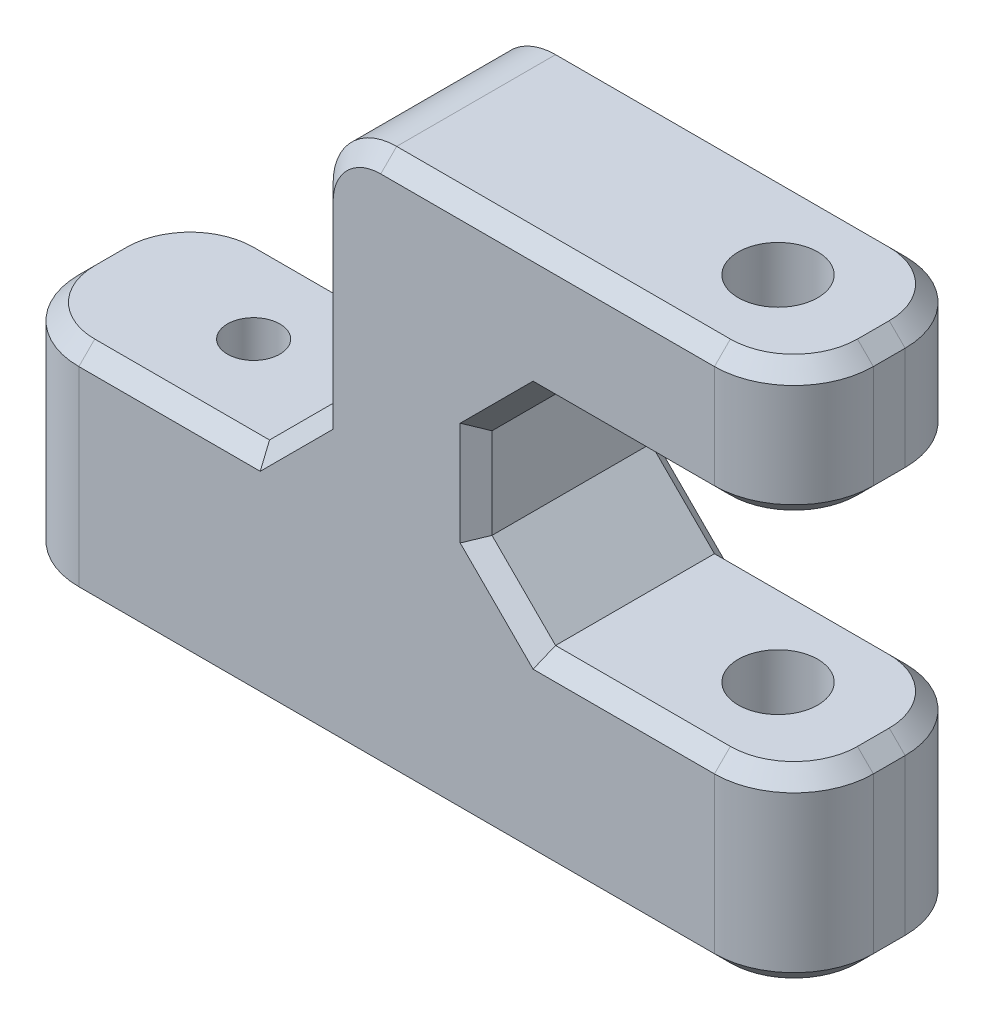
SolidWorks part; units mm, degrees
material "PLA"
ref_plane "Front Plane" through (0, 0, 0) normal (0, 0, 1) x (1, 0, 0)
ref_plane "Top Plane" through (0, 0, 0) normal (0, 1, 0) x (1, 0, 0)
ref_plane "Right Plane" through (0, 0, 0) normal (1, 0, 0) x (0, 0, -1)
sketch "Sketch1" plane through (0, 0, 0) normal (0, 0, 1) x (1, 0, 0)
  line L0 (0, 14) -> (0, 34)
  line L1 (0, 34) -> (30, 34)
  line L2 (30, 34) -> (30, 25.5)
  line L3 (30, 25.5) -> (10, 25.5)
  line L4 (10, 25.5) -> (10, 11.8)
  line L5 (10, 11.8) -> (30, 11.8)
  line L6 (30, 11.8) -> (30, 0)
  line L7 (30, 0) -> (0, 0)
  line L8 (2.9482, 34) -> (2.9482, 0) construction
  line L9 (0, 14) -> (-20, 14)
  line L10 (-20, 14) -> (-20, 0)
  line L11 (-20, 0) -> (0, 0)
  line L12 (2.9482, 18.65) -> (37.0838, 18.65) construction
  point P16 (10, 18.65)
  point P17 (0, 0)
  dimension "D1" = 34
  dimension "D2" = 13.7
  dimension "D3" = 10
  dimension "D4" = 30
  dimension "D5" = 20
  dimension "D6" = 20
extrude "Boss-Extrude1" add sketch "Sketch1" along normal mid plane 12
sketch "Sketch2" plane through (0, 14, 0) normal (0, 1, 0) x (1, 0, 0)
  line L0 (0, 0) -> (-20, 0) construction
  line L1 (-20, -6) -> (-20, 6) construction
  circle A0 centre (-10, 0) radius 1.65
  dimension "D1" = 3.3
extrude "Cut-Extrude1" cut sketch "Sketch2" against normal blind 20
sketch "Sketch3" plane through (0, 11.8, 0) normal (0, 1, 0) x (1, 0, 0)
  line L0 (30, 0) -> (0, 0) construction
  line L1 (30, -6) -> (30, 6) construction
  circle A0 centre (23, 0) radius 2.5
  dimension "D2" = 5
  dimension "D1" = 7
extrude "Cut-Extrude2" cut sketch "Sketch3" against normal mid plane 60
chamfer "Chamfer1" distance 4 angle 45 3 edges at (0, 14, 0) (10, 11.8, 0) (10, 25.5, 0)
fillet "Fillet1" radius 4 1 edges at (0, 34, 0)
fillet "Fillet2" radius 5 6 edges at (30, 5.9, -6) (30, 5.9, 6) (-20, 7, -6) (-20, 7, 6) (30, 29.75, -6) (30, 29.75, 6)
chamfer "Chamfer2" distance 1 angle 45 40 edges at (-18.5355, 0, 4.5355) (-20, 0, 0) (5, 0, 6) (-18.5355, 0, -4.5355) (28.5355, 0, 4.5355) (5, 0, -6) (30, 0, 0) (28.5355, 0, -4.5355) (12, 23.5, -6) (10, 18.65, -6) (12, 13.8, -6) (19.5, 25.5, -6) (19.5, 11.8, -6) (28.5355, 25.5, -4.5355) (28.5355, 11.8, -4.5355) (30, 25.5, 0) (30, 11.8, 0) (28.5355, 25.5, 4.5355) (28.5355, 11.8, 4.5355) (19.5, 25.5, 6) (12, 23.5, 6) (10, 18.65, 6) (12, 13.8, 6) (19.5, 11.8, 6) (-2, 16, -6) (-9.5, 14, -6) (-18.5355, 14, -4.5355) (-20, 14, 0) (-18.5355, 14, 4.5355) (-9.5, 14, 6) (-2, 16, 6) (0, 24, -6) (1.1716, 32.8284, -6) (14.5, 34, -6) (28.5355, 34, -4.5355) (30, 34, 0) (0, 24, 6) (28.5355, 34, 4.5355) (1.1716, 32.8284, 6) (14.5, 34, 6)
